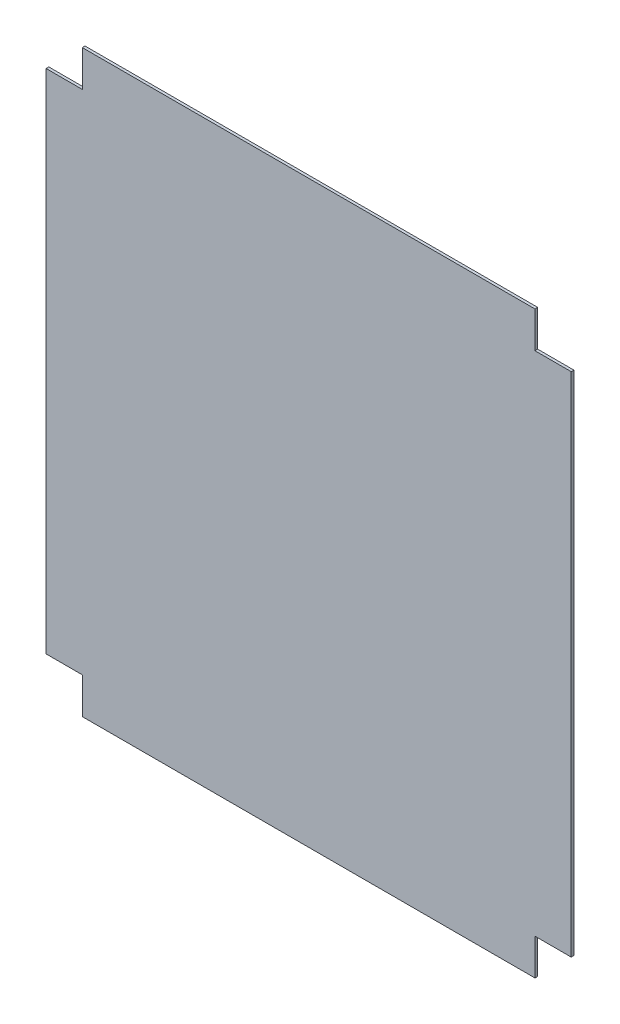
SolidWorks part; units mm, degrees
ref_plane "Plan de face" through (0, 0, 0) normal (0, 0, 1) x (1, 0, 0)
ref_plane "Plan de dessus" through (0, 0, 0) normal (0, 1, 0) x (1, 0, 0)
ref_plane "Plan de droite" through (0, 0, 0) normal (1, 0, 0) x (0, 0, -1)
sketch "Esquisse1" plane through (0, 0, 0) normal (0, 0, 1) x (1, 0, 0)
  line L1 (-240, -250) -> (260, -250)
  line L2 (-280, -210) -> (-280, 350)
  line L3 (-240, 390) -> (260, 390)
  line L4 (300, -210) -> (300, 350)
  line L5 (-240, -214.2857) -> (260, 232.1429) construction
  line L6 (-240, 214.2857) -> (260, -232.1429) construction
  line L9 (-280, 350) -> (-240, 350)
  line L10 (-240, 390) -> (-240, 350)
  line L13 (300, 350) -> (260, 350)
  line L14 (260, 390) -> (260, 350)
  line L17 (-280, -210) -> (-240, -210)
  line L18 (-240, -250) -> (-240, -210)
  line L21 (300, -210) -> (260, -210)
  line L22 (260, -250) -> (260, -210)
  point P0 (0, 0)
  dimension "D2" = 640
  dimension "D3" = 40
  dimension "D4" = 40
  dimension "D5" = 40
  dimension "D6" = 40
  dimension "D7" = 40
  dimension "D8" = 40
  dimension "D9" = 40
  dimension "D10" = 40
  dimension "D11" = 580
extrude "Boss.-Extru.1" add sketch "Esquisse1" along normal blind 3
